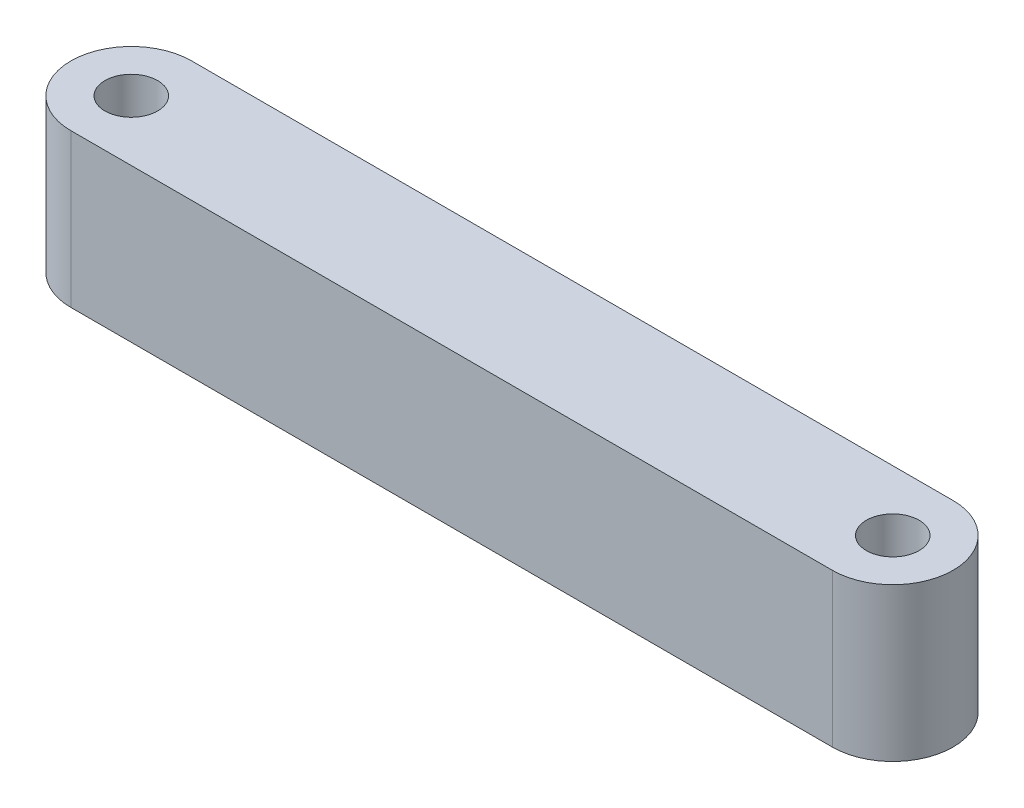
SolidWorks part; units mm, degrees
ref_plane "Front Plane" through (0, 0, 0) normal (0, 0, 1) x (1, 0, 0)
ref_plane "Top Plane" through (0, 0, 0) normal (0, 1, 0) x (1, 0, 0)
ref_plane "Right Plane" through (0, 0, 0) normal (1, 0, 0) x (0, 0, -1)
sketch "Sketch1" plane through (0, 0, 0) normal (0, 1, 0) x (1, 0, 0)
  line L0 (-22.945, 0) -> (21.81, 0) construction
  line L1 (-22.945, 3.55) -> (21.81, 3.55)
  line L2 (-22.945, -3.55) -> (21.81, -3.55)
  circle A0 centre (-22.945, 0) radius 1.55
  circle A1 centre (21.81, 0) radius 1.55
  arc A2 (-22.945, 3.55) -> (-22.945, -3.55) centre (-22.945, 0) ccw
  arc A3 (21.81, -3.55) -> (21.81, 3.55) centre (21.81, 0) ccw
  point P4 (-0.5675, 0)
  dimension "D2" = 3.1
  dimension "D3" = 2
  dimension "D1" = 44.755
extrude "Boss-Extrude1" add sketch "Sketch1" along normal blind 9
